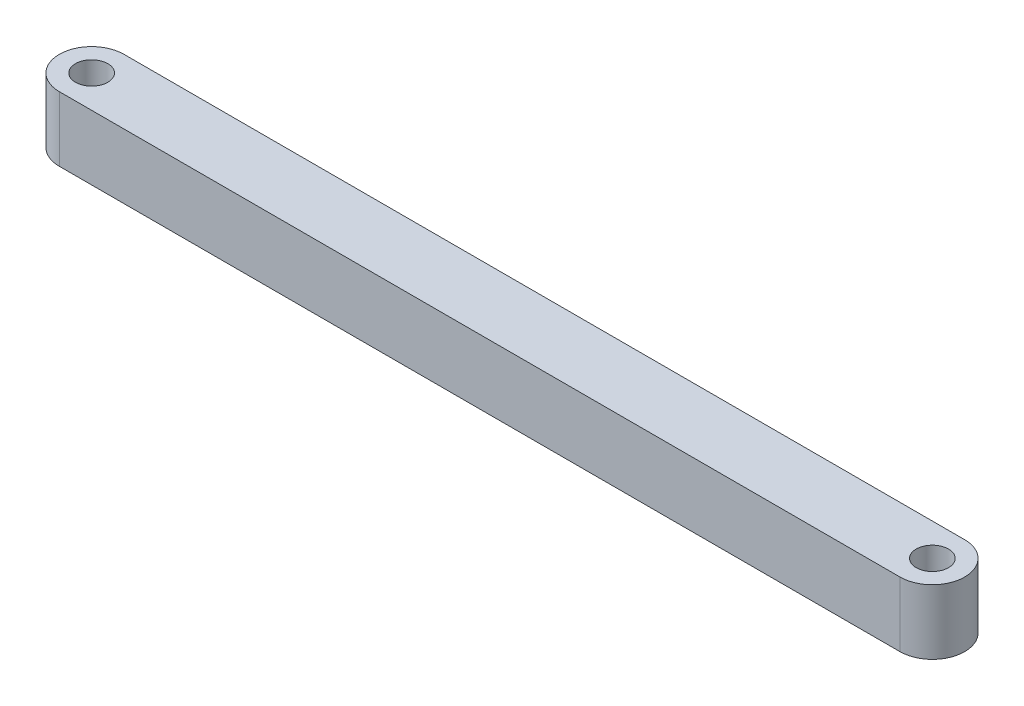
SolidWorks part; units mm, degrees
material "Rod"
ref_plane "Front Plane" through (0, 0, 0) normal (0, 0, 1) x (1, 0, 0)
ref_plane "Top Plane" through (0, 0, 0) normal (0, 1, 0) x (1, 0, 0)
ref_plane "Right Plane" through (0, 0, 0) normal (1, 0, 0) x (0, 0, -1)
sketch "Sketch2" plane through (0, 0, 0) normal (0, 1, 0) x (1, 0, 0)
  line L0 (-65, -5) -> (65, -5)
  line L1 (-65, 5) -> (65, 5)
  line L2 (0, 0) -> (86.1163, 0) construction
  line L3 (0, 0) -> (-97.4436, 0) construction
  line L4 (0, 0) -> (0, -41.2201) construction
  line L5 (0, 0) -> (0, 30.7571) construction
  arc A0 (65, -5) -> (65, 5) centre (65, 0) ccw
  arc A1 (-65, -5) -> (-65, 5) centre (-65, 0) cw
  circle A2 centre (-65, 0) radius 2.5
  circle A3 centre (65, 0) radius 2.5
  dimension "D3" = 5
  dimension "D4" = 5
  dimension "D5" = 5
  dimension "D6" = 5
  dimension "D1" = 65
  dimension "D2" = 130
  dimension "D7" = 130
  dimension "D8" = 65
  dimension "D9" = 5
  dimension "D10" = 10
  dimension "D11" = 10
  dimension "D12" = 10
extrude "Boss-Extrude2" add sketch "Sketch2" along normal blind 10
